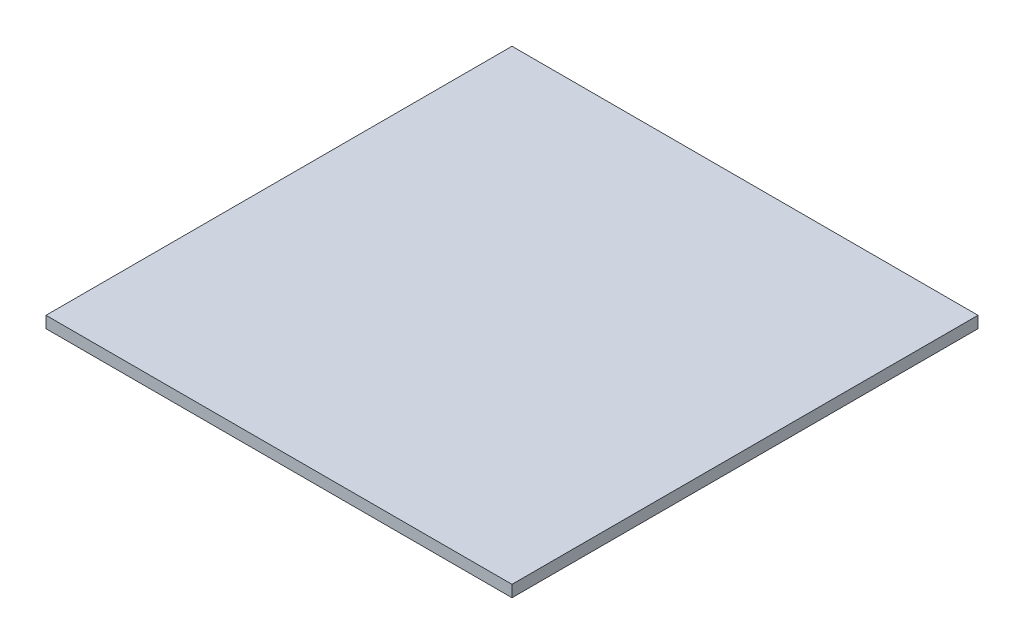
SolidWorks part; units mm, degrees
ref_plane "前视基准面" through (0, 0, 0) normal (0, 0, 1) x (1, 0, 0)
ref_plane "上视基准面" through (0, 0, 0) normal (0, 1, 0) x (1, 0, 0)
ref_plane "右视基准面" through (0, 0, 0) normal (1, 0, 0) x (0, 0, -1)
sketch "草图1" plane through (0, 0, 0) normal (0, 1, 0) x (1, 0, 0)
  line L1 (-40, 40) -> (40, 40)
  line L2 (-40, 40) -> (-40, -40)
  line L3 (-40, -40) -> (40, -40)
  line L4 (40, 40) -> (40, -40)
  line L5 (-40, 40) -> (40, -40) construction
  line L6 (-40, -40) -> (40, 40) construction
  point P0 (0, 0)
  dimension "D1" = 80
  dimension "D2" = 80
extrude "凸台-拉伸1" add sketch "草图1" along normal blind 2
